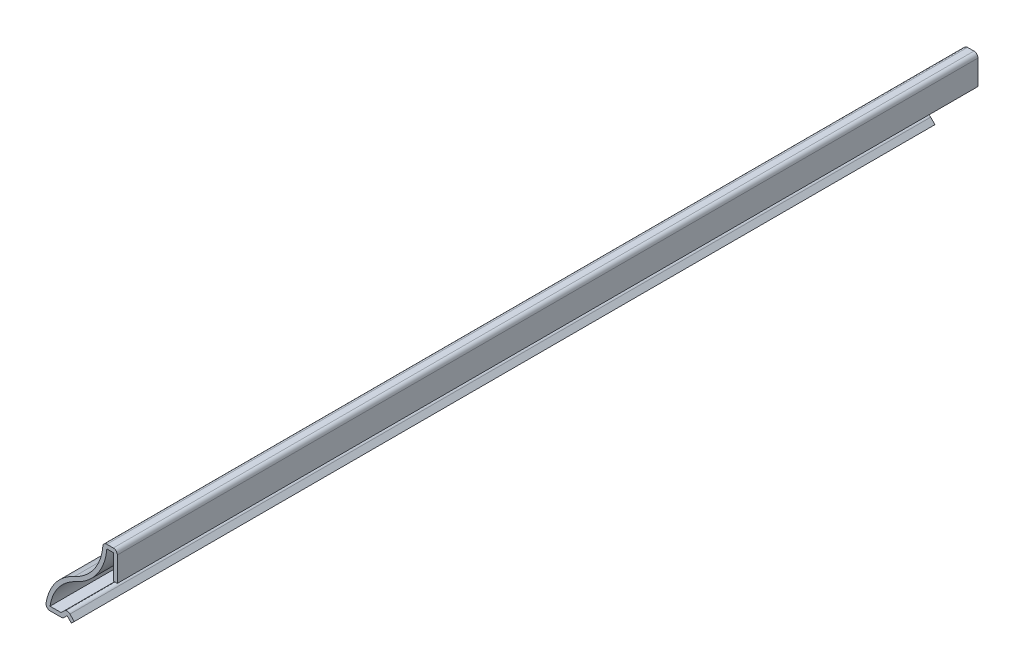
SolidWorks part; units mm, degrees
ref_plane "Front Plane" through (0, 0, 0) normal (0, 0, 1) x (1, 0, 0)
ref_plane "Top Plane" through (0, 0, 0) normal (0, 1, 0) x (1, 0, 0)
ref_plane "Right Plane" through (0, 0, 0) normal (1, 0, 0) x (0, 0, -1)
sketch "Sketch1" plane through (0, 0, 0) normal (0, 0, 1) x (1, 0, 0)
  line L0 (0, 0) -> (-0.9589, 0.9589)
  line L1 (-0.9589, 0.9589) -> (-1.9178, 0)
  line L2 (-1.9178, 0) -> (-5.7214, 0)
  line L3 (6.9786, 19.05) -> (10.1536, 19.05)
  line L4 (10.1536, 19.05) -> (10.1536, 12.7)
  line L5 (0.6286, 0.6286) -> (-0.9589, 2.2161)
  line L6 (-0.9589, 2.2161) -> (-2.286, 0.889)
  line L7 (-2.286, 0.889) -> (-4.7427, 0.889)
  line L8 (7.8335, 18.161) -> (9.2646, 18.161)
  line L9 (9.2646, 18.161) -> (9.2646, 12.7)
  line L10 (9.2646, 12.7) -> (10.1536, 12.7)
  line L11 (0, 0) -> (0.6286, 0.6286)
  line L12 (-1.9178, 0) -> (0, 0) construction
  arc A0 (-5.7214, 0) -> (0.6221, 9.2611) centre (4.9812, -0.5278) cw
  arc A1 (0.6221, 9.2611) -> (6.9786, 19.05) centre (-3.737, 19.05) ccw
  arc A2 (-4.7427, 0.889) -> (0.9838, 8.449) centre (4.9812, -0.5278) cw
  arc A3 (0.9838, 8.449) -> (7.8335, 18.161) centre (-3.737, 19.05) ccw
  point P9 (0, 0)
  point P12 (-0.9589, 0)
  point P13 (0.9765, 8.1953)
  point P24 (0, 0)
  dimension "D5" = 10.7156
  dimension "D1" = 19.05
  dimension "D2" = 15.875
  dimension "D3" = 3.175
  dimension "D4" = 6.35
  dimension "D7" = 6.35
  dimension "D8" = 1.5875
  dimension "D6" = 0.889
extrude "Boss-Extrude1" add sketch "Sketch1" against normal blind 190.5
fillet "Fillet1" radius 0.889 5 edges at (-1.9178, 0, -95.25) (-0.9589, 2.2161, -95.25) (-5.7214, 0, -95.25) (6.9786, 19.05, -95.25) (10.1536, 19.05, -95.25)
